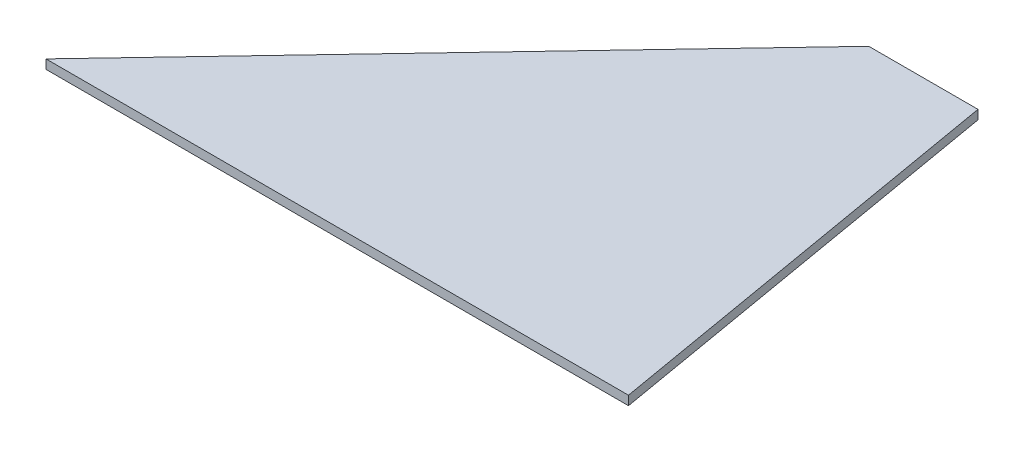
SolidWorks part; units mm, degrees
material "Balsa"
ref_plane "Front Plane" through (0, 0, 0) normal (0, 0, 1) x (1, 0, 0)
ref_plane "Top Plane" through (0, 0, 0) normal (0, 1, 0) x (1, 0, 0)
ref_plane "Right Plane" through (0, 0, 0) normal (1, 0, 0) x (0, 0, -1)
sketch "Sketch1" plane through (0, 0, 0) normal (0, 1, 0) x (1, 0, 0)
  line L0 (0, 0) -> (0, 147.32)
  line L1 (0, 147.32) -> (-63.5, 147.32)
  line L2 (-63.5, 147.32) -> (-203.2, 0)
  line L3 (-203.2, 0) -> (0, 0)
  line L4 (0, 0) -> (-25.4, 147.32)
  dimension "D1" = 203.2
  dimension "D2" = 147.32
  dimension "D3" = 63.5
  dimension "D4" = 25.4
extrude "Boss-Extrude1" add sketch "Sketch1" along normal blind 3.175 contours L3 L4 L1 L2
